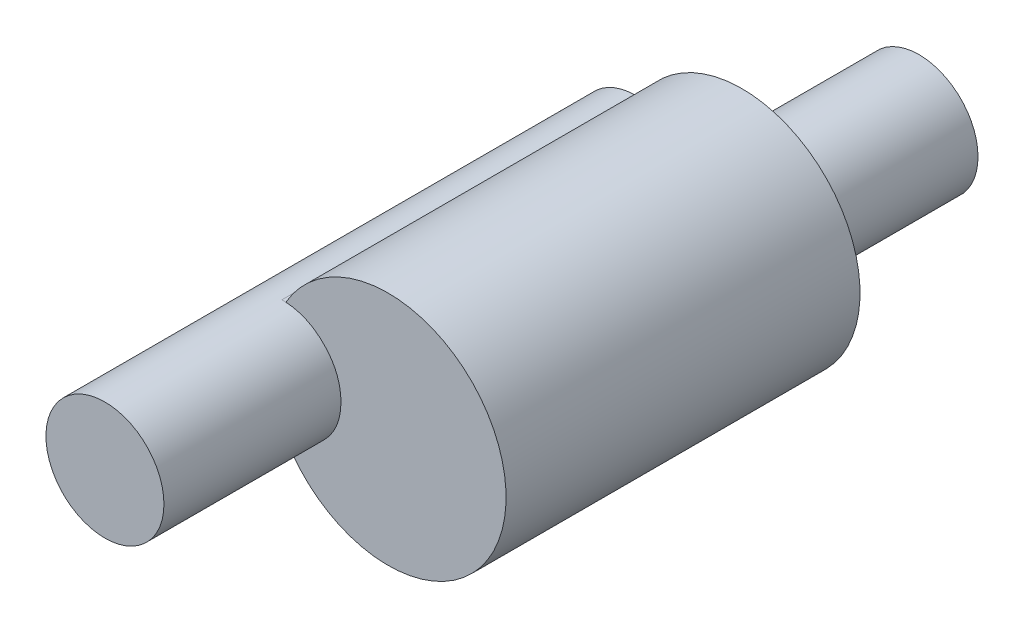
SolidWorks part; units mm, degrees
ref_plane "Спереди" through (0, 0, 0) normal (0, 0, 1) x (1, 0, 0)
ref_plane "Сверху" through (0, 0, 0) normal (0, 1, 0) x (1, 0, 0)
ref_plane "Справа" through (0, 0, 0) normal (1, 0, 0) x (0, 0, -1)
other "Configuration Table"
sketch "Sketch1" plane through (0, 0, 0) normal (0, 0, 1) x (1, 0, 0)
  line L0 (6.2799, 7.8479) -> (-8.0198, 7.8479) construction
  line L1 (-6.8342, 8.8479) -> (-6.7663, 8.8479)
  line L2 (-6.8342, 6.8479) -> (-6.7663, 6.8479)
  arc A0 (-6.8342, 8.8479) -> (-6.8342, 6.8479) centre (-6.8342, 7.8479) ccw
  arc A1 (-6.7663, 6.8479) -> (-6.7663, 8.8479) centre (-5.0342, 7.8479) ccw
  arc A2 (-6.8342, 6.8479) -> (-5.8342, 7.8479) centre (-6.8342, 7.8479) ccw construction
  arc A3 (-5.8342, 7.8479) -> (-6.8342, 8.8479) centre (-6.8342, 7.8479) ccw construction
  arc A4 (-6.7663, 6.8479) -> (-7.0342, 7.8479) centre (-5.0342, 7.8479) cw construction
  arc A5 (-7.0342, 7.8479) -> (-6.7663, 8.8479) centre (-5.0342, 7.8479) cw construction
  dimension "D1" = 2
  dimension "D3" = 4
  dimension "D2" = 2
  dimension "D4" = 1.8
extrude "Boss-Extrude1" add sketch "Sketch1" along normal blind 6
ref_plane "Plane1" through (0, 0, 6) normal (0, 0, 1) x (1, 0, 0)
sketch "Sketch2" plane through (0, 0, 6) normal (0, 0, 1) x (1, 0, 0)
  circle A0 centre (-6.8342, 7.8479) radius 1
  arc A1 (-6.8342, 8.8479) -> (-6.8342, 6.8479) centre (-6.8342, 7.8479) ccw construction
extrude "Boss-Extrude2" add sketch "Sketch2" along normal blind 3
ref_plane "Plane2" through (0, 0, 0) normal (0, 0, -1) x (-1, 0, 0)
sketch "Sketch3" plane through (0, 0, 0) normal (0, 0, -1) x (-1, 0, 0)
  circle A0 centre (5.0342, 7.8479) radius 1
  circle A1 centre (6.8342, 7.8479) radius 1 construction
extrude "Boss-Extrude3" add sketch "Sketch3" along normal blind 3
equation "\"R small\"= 2"
equation "\"R big\"= 4"
equation "\"width\"= 0.6"
equation "\"border width\"= 1"
equation "\"D3@Sketch1\"=\"R big\""
equation "\"D2@Sketch1\"=\"R small\""
equation "\"D1@Sketch1\"=\"R small\""
equation "\"depth\"= 3"
